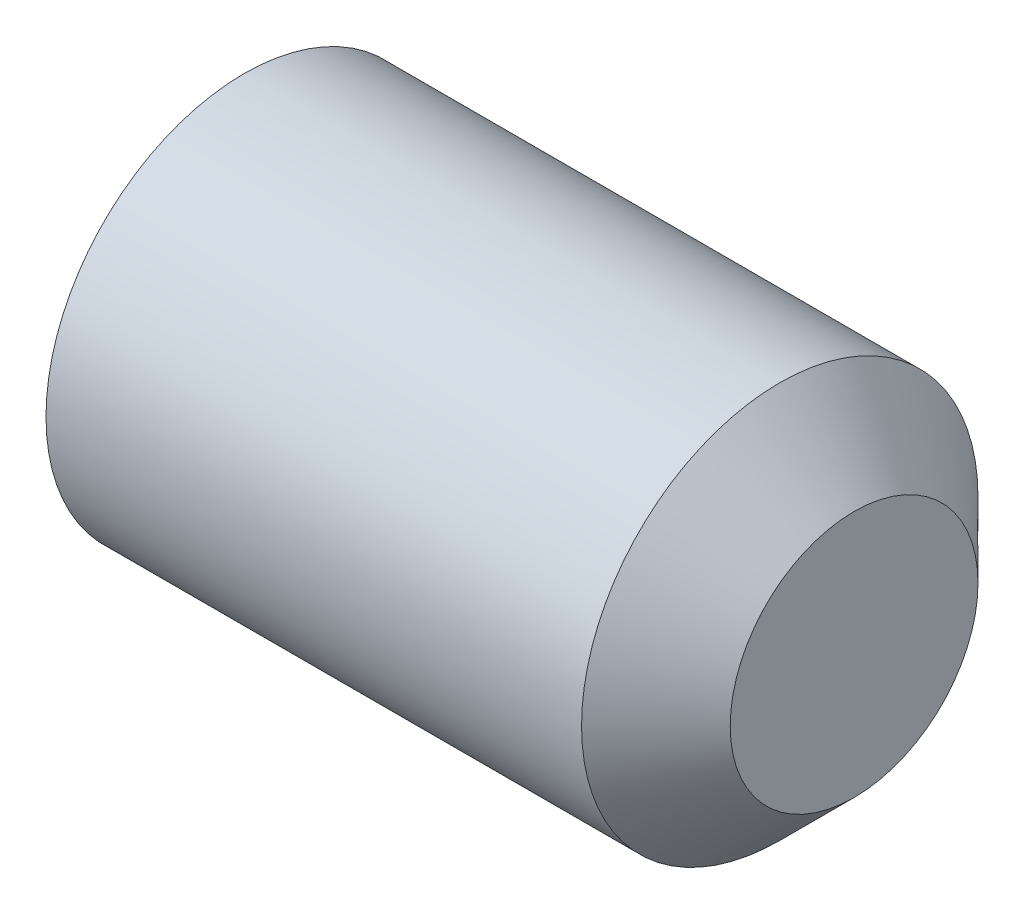
SolidWorks part; units mm, degrees
ref_plane "Спереди" through (0, 0, 0) normal (0, 0, 1) x (1, 0, 0)
ref_plane "Сверху" through (0, 0, 0) normal (0, 1, 0) x (1, 0, 0)
ref_plane "Справа" through (0, 0, 0) normal (1, 0, 0) x (0, 0, -1)
ref_plane "Плоскость1" through (0, 0, 0) normal (0, 0, -1) x (-1, 0, 0)
sketch "Эскиз1" plane through (0, 0, 0) normal (0, 0, -1) x (-1, 0, 0)
  line L0 (-6.5, 2) -> (-6.5, 0)
  line L1 (-6.5, 0) -> (0, 0)
  line L2 (0, 0) -> (0, 2)
  line L3 (0, 2) -> (-6.5, 2)
  line L4 (-6.5, 0) -> (0, 0) construction
  dimension "D1" = 2
  dimension "D2" = 6.5
revolve "Повернуть1" add sketch "Эскиз1" angle 360 about L4
sketch "Эскиз2" plane through (0, 0, 0) normal (-1, 0, 0) x (0, 0, 1)
  line L0 (1.1547, 0) -> (0.5774, 1)
  line L1 (0.5774, 1) -> (-0.5774, 1)
  line L2 (-0.5774, 1) -> (-1.1547, 0)
  line L3 (-1.1547, 0) -> (-0.5774, -1)
  line L4 (-0.5774, -1) -> (0.5774, -1)
  line L5 (0.5774, -1) -> (1.1547, 0)
extrude "Вырез-Вытянуть1" cut sketch "Эскиз2" against normal blind 1.5
chamfer "Фаска1" distance 0.75 angle 45 1 edges at (6.5, -2, 0)
chamfer "Фаска2" distance 0.6 angle 30 1 edges at (0, -2, 0)
fillet "Скругление1" radius 0.1 13 edges at (1.5, -1, 0) (1.5, -0.5, -0.866) (1.5, 0.5, -0.866) (1.5, 1, 0) (1.5, 0.5, 0.866) (1.5, -0.5, 0.866) (0, 0.5, 0.866) (0, 1, 0) (0, 0.5, -0.866) (0, -0.5, -0.866) (0, -1, 0) (0, -0.5, 0.866) (0, -1.4, 0)
